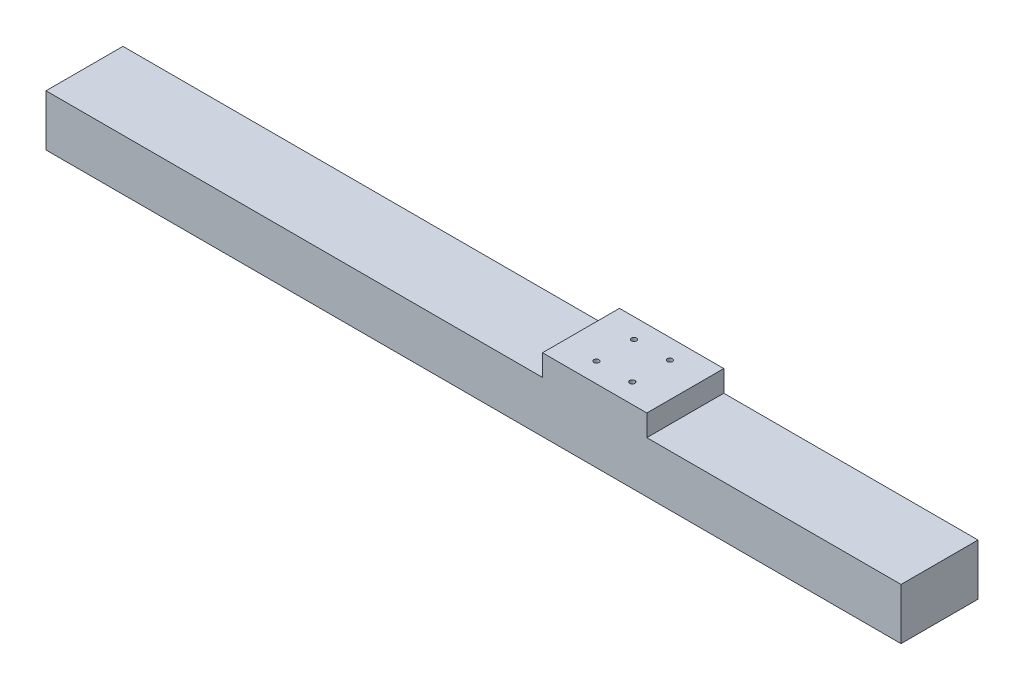
SolidWorks part; units mm, degrees
ref_plane "Front Plane" through (0, 0, 0) normal (0, 0, 1) x (1, 0, 0)
ref_plane "Top Plane" through (0, 0, 0) normal (0, 1, 0) x (1, 0, 0)
ref_plane "Right Plane" through (0, 0, 0) normal (1, 0, 0) x (0, 0, -1)
sketch "Sketch1" plane through (0, 0, 0) normal (0, 1, 0) x (1, 0, 0)
  line L1 (-125.3055, 0) -> (874.6945, 0)
  line L2 (-125.3055, 0) -> (-125.3055, -90)
  line L3 (-125.3055, -90) -> (874.6945, -90)
  line L4 (874.6945, 0) -> (874.6945, -90)
  dimension "D1" = 90
  dimension "D2" = 1000
extrude "Boss-Extrude1" add sketch "Sketch1" along normal blind 60
sketch "Sketch2" plane through (0, 60, 0) normal (0, 1, 0) x (1, 0, 0)
  line L0 (874.6945, 0) -> (-125.3055, 0) construction
  line L1 (455.3822, 0) -> (577.3822, 0)
  line L2 (455.3822, 0) -> (455.3822, -90)
  line L3 (455.3822, -90) -> (577.3822, -90)
  line L4 (577.3822, 0) -> (577.3822, -90)
  line L5 (-125.3055, -90) -> (874.6945, -90) construction
  dimension "D1" = 122
extrude "Boss-Extrude2" add sketch "Sketch2" along normal blind 25
sketch "Sketch3" plane through (0, 85, 0) normal (0, 1, 0) x (1, 0, 0)
  line L0 (455.3822, -45) -> (561.5078, -45) construction
  line L1 (455.3822, 0) -> (455.3822, -90) construction
  line L2 (516.3822, 0) -> (516.3822, -60.6081) construction
  line L3 (577.3822, 0) -> (455.3822, 0) construction
  circle A0 centre (495.3822, -23) radius 3
  circle A1 centre (537.3822, -23) radius 3
  circle A2 centre (537.3822, -67) radius 3
  circle A3 centre (495.3822, -67) radius 3
  dimension "D1" = 6
  dimension "D2" = 42
  dimension "D3" = 44
extrude "Cut-Extrude1" cut sketch "Sketch3" against normal blind 10
